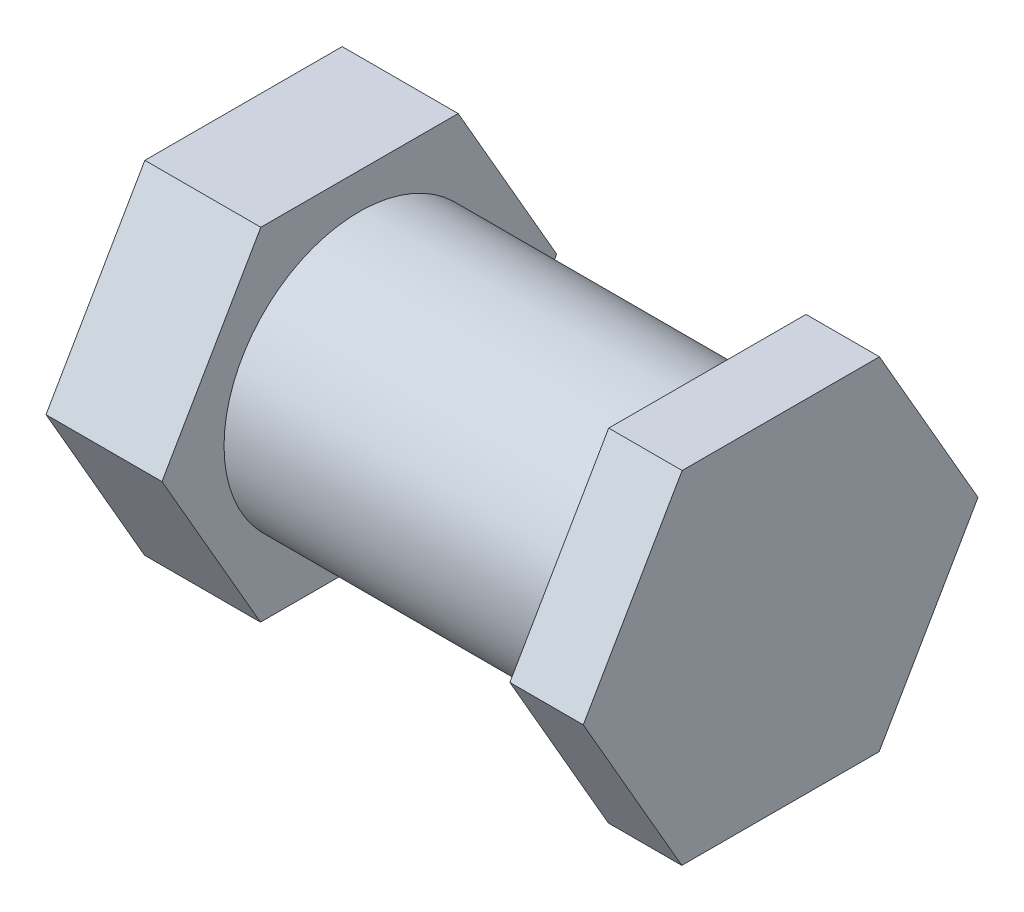
SolidWorks part; units mm, degrees
ref_plane "Front Plane" through (0, 0, 0) normal (0, 0, 1) x (1, 0, 0)
ref_plane "Top Plane" through (0, 0, 0) normal (0, 1, 0) x (1, 0, 0)
ref_plane "Right Plane" through (0, 0, 0) normal (1, 0, 0) x (0, 0, -1)
sketch "Sketch1" plane through (64.4682, 0, 0) normal (-1, 0, 0) x (0, 0, 1)
  circle A0 centre (260.8616, 7.55) radius 3.5
  dimension "D1" = 7
extrude "Boss-Extrude1" add sketch "Sketch1" against normal blind 9 and the other way blind 3
sketch "Sketch2" plane through (61.4682, 0, 0) normal (-1, 0, 0) x (0, 0, 1)
  line L9 (263.4189, 3.1308) -> (265.9674, 7.5551)
  line L10 (265.9674, 7.5551) -> (263.4102, 11.9743)
  line L11 (263.4102, 11.9743) -> (258.3043, 11.9692)
  line L12 (258.3043, 11.9692) -> (255.7558, 7.5449)
  line L13 (255.7558, 7.5449) -> (258.3131, 3.1257)
  line L14 (258.3131, 3.1257) -> (263.4189, 3.1308)
  circle A0 centre (260.8616, 7.55) radius 4.4218 construction
extrude "Boss-Extrude2" add sketch "Sketch2" against normal up to surface (3 mm away)
sketch "Sketch3" plane through (73.4682, 0, 0) normal (1, 0, 0) x (0, 0, -1)
  line L9 (-258.3131, 3.1257) -> (-255.7558, 7.5449)
  line L10 (-255.7558, 7.5449) -> (-258.3043, 11.9692)
  line L11 (-258.3043, 11.9692) -> (-263.4102, 11.9743)
  line L12 (-263.4102, 11.9743) -> (-265.9674, 7.5551)
  line L13 (-265.9674, 7.5551) -> (-263.4189, 3.1308)
  line L14 (-263.4189, 3.1308) -> (-258.3131, 3.1257)
  circle A0 centre (-260.8616, 7.55) radius 4.4218 construction
extrude "Boss-Extrude3" add sketch "Sketch3" along normal blind 1.9
